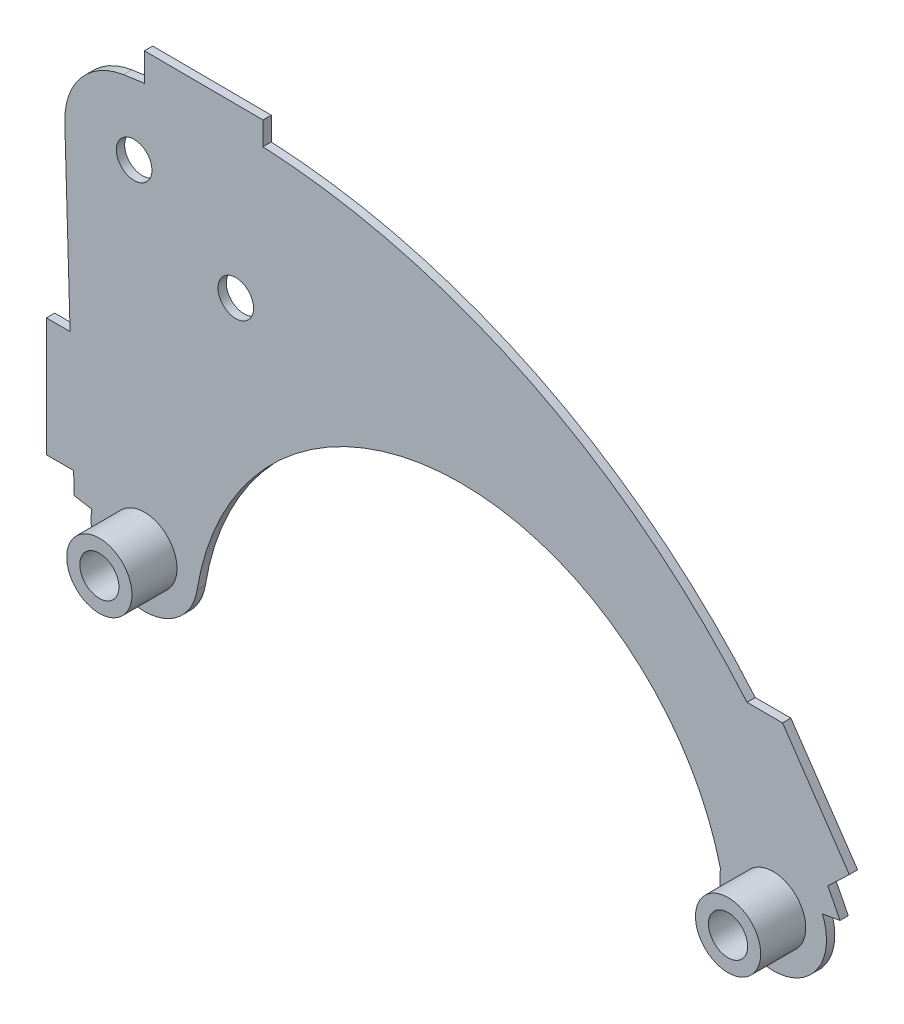
SolidWorks part; units mm, degrees
ref_plane "Front Plane" through (0, 0, 0) normal (0, 0, 1) x (1, 0, 0)
ref_plane "Top Plane" through (0, 0, 0) normal (0, 1, 0) x (1, 0, 0)
ref_plane "Right Plane" through (0, 0, 0) normal (1, 0, 0) x (0, 0, -1)
sketch "Sketch1" plane through (0, 0, 0) normal (0, 0, 1) x (1, 0, 0)
  line L0 (3.5714, 20.1522) -> (3.5714, -246.7943) construction
  line L1 (-308.017, 51.5444) -> (-322.8113, 54.0201)
  line L2 (3.2114, 1.0414) -> (684.3791, 1.0414) construction
  line L3 (3.2114, 1.0414) -> (-642.1053, 1.0414) construction
  line L4 (3.2114, 1.0414) -> (3.2114, 295.5408) construction
  line L5 (266.5683, 46.7848) -> (266.5683, 1.7848) construction
  line L6 (3.2114, 1.0414) -> (3.5714, 1.1081) construction
  line L7 (-263.6341, 44.1172) -> (-263.6341, -0.8828) construction
  line L8 (308.1159, 64.0706) -> (322.9429, 66.6583)
  line L9 (-263.6341, -0.8828) -> (3.2114, 1.0414)
  line L10 (-322.8113, 54.0201) -> (-330.7613, 322.7691)
  line L11 (3.2114, 1.0414) -> (3.5714, 1.1081)
  arc A0 (222.17, 54.1191) -> (-219.2092, 36.9459) centre (3.2114, 1.0414) ccw
  arc A1 (-308.017, 51.5444) -> (-219.2092, 36.9459) centre (-263.6341, 44.1172) ccw
  arc A4 (222.17, 54.1191) -> (308.1159, 64.0706) centre (266.5683, 46.7848) ccw
  circle A5 centre (-263.6341, 44.1172) radius 16.5
  circle A6 centre (266.5683, 46.7848) radius 16.5
  circle A9 centre (3.2114, 1.0414) radius 217.3
  arc A11 (-281.3271, 382.2962) -> (-330.7613, 322.7691) centre (-272.2869, 324.4989) ccw
  circle A12 centre (-272.2869, 324.4989) radius 15
  arc A14 (322.9429, 66.6583) -> (-281.3271, 382.2962) centre (-192.7071, -184.2846) ccw
  circle A15 centre (-186.5844, 266.4702) radius 15
  dimension "D1" = 90
  dimension "D2" = 0.413
  dimension "D5" = 10.5
  dimension "D6" = 267.3
extrude "Boss-Extrude3" add sketch "Sketch1" along normal blind 7 contours L8 A14 A11 A15 L10 L1 A1 A0 A4 A5 A6 | A11 A12
sketch "Sketch2" plane through (0, 0, 7) normal (0, 0, 1) x (1, 0, 0)
  circle A0 centre (-263.6341, 44.1172) radius 27.5
  circle A2 centre (-263.6341, 44.1172) radius 16.5
  circle A3 centre (266.5683, 46.7848) radius 16.5
  circle A4 centre (266.5683, 46.7848) radius 27.5
extrude "Boss-Extrude4" add sketch "Sketch2" along normal blind 38
sketch "Sketch3" plane through (0, 0, 7) normal (0, 0, 1) x (1, 0, 0)
  line L0 (-263.6341, 44.1172) -> (-263.6341, 453.1062) construction
  line L8 (-263.6341, 408.5417) -> (-263.6341, 384.2673)
  line L9 (-163.6355, 408.0299) -> (-163.6355, 388.0299)
  line L10 (-263.6341, 384.2673) -> (-163.6355, 388.0299)
  line L11 (-326.3061, 172.1603) -> (-346.3061, 172.1603)
  line L12 (-346.3061, 172.1603) -> (-346.3061, 72.1603)
  line L13 (-346.3061, 72.1603) -> (-323.3479, 72.1603)
  line L14 (-322.8113, 54.0201) -> (-330.7613, 322.7691) construction
  line L15 (-323.3479, 72.1603) -> (-326.3061, 172.1603)
  line L16 (266.5683, 46.7848) -> (389.2154, 46.7848) construction
  line L17 (266.5683, 46.7848) -> (266.5683, 243.9392) construction
  line L18 (244.5283, 186.7848) -> (312.6529, 86.7848)
  line L20 (274.5283, 186.7848) -> (244.5283, 186.7848)
  line L22 (-263.6341, 44.1172) -> (-111.3913, 44.1172) construction
  line L23 (-263.6341, 408.5417) -> (-163.6355, 408.0299)
  line L24 (274.5283, 186.7848) -> (330.8297, 104.14)
  line L25 (330.8297, 104.14) -> (312.6529, 86.7848)
  arc A1 (322.9429, 66.6583) -> (-281.3271, 382.2962) centre (-192.7071, -184.2846) ccw construction
  dimension "D1" = 128.0431
extrude "Boss-Extrude5" add sketch "Sketch3" against normal up to surface (7 mm away) up to face at (-171.5844, 266.4702, 0)
